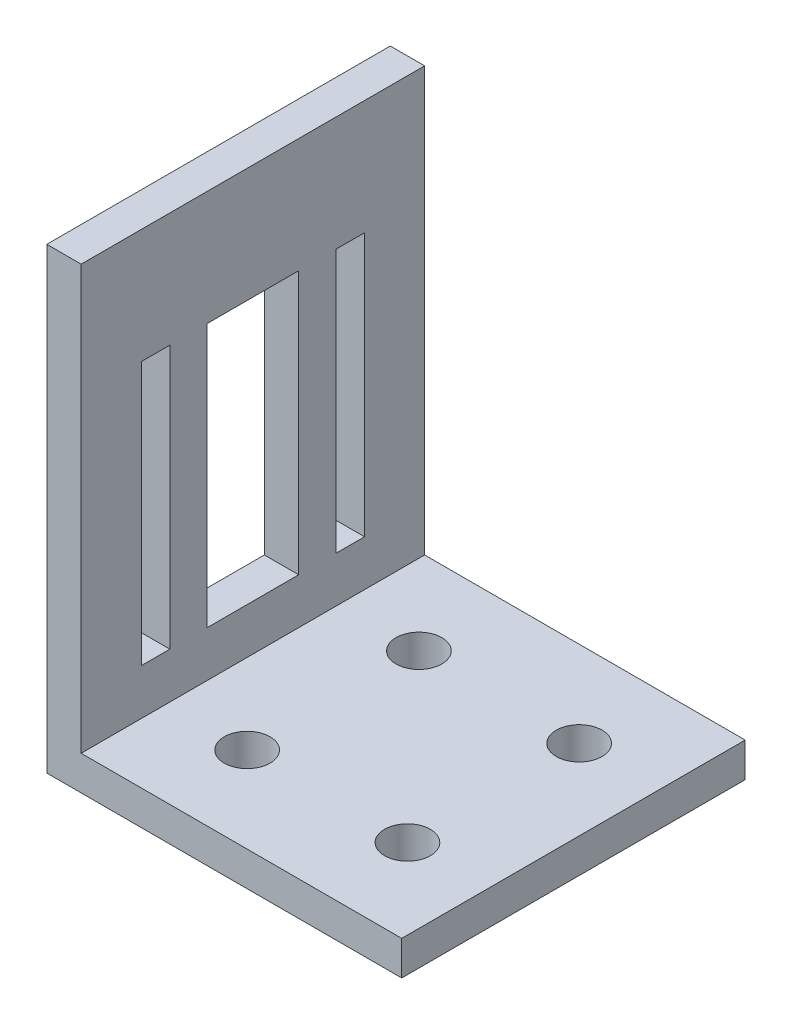
SolidWorks part; units mm, degrees
ref_plane "Front Plane" through (0, 0, 0) normal (0, 0, 1) x (1, 0, 0)
ref_plane "Top Plane" through (0, 0, 0) normal (0, 1, 0) x (1, 0, 0)
ref_plane "Right Plane" through (0, 0, 0) normal (1, 0, 0) x (0, 0, -1)
sketch "Sketch2" plane through (0, 0, 0) normal (0, 0, 1) x (1, 0, 0)
  line L0 (0, 0) -> (-31, 0)
  line L1 (-31, 0) -> (-31, 40)
  line L2 (0, 3) -> (-28, 3)
  line L3 (-28, 3) -> (-28, 40)
  line L4 (-28, 40) -> (-31, 40)
  line L5 (0, 0) -> (0, 3)
  dimension "D1" = 31
  dimension "D2" = 3
extrude "Boss-Extrude1" add sketch "Sketch2" along normal blind 30
sketch "Sketch3" plane through (0, 3, 0) normal (0, 1, 0) x (1, 0, 0)
  line L0 (-28, -15) -> (0, -15) construction
  line L1 (-14, -15) -> (0, -30) construction
  line L2 (-14, -30) -> (0, -15) construction
  line L5 (-28, -30) -> (-28, 0) construction
  line L6 (0, -30) -> (0, 0) construction
  line L7 (-14, 0) -> (-14, -30) construction
  line L8 (0, 0) -> (-28, 0) construction
  line L9 (0, -30) -> (-28, -30) construction
  circle A0 centre (-7, -22.5) radius 2
  circle A1 centre (-21, -22.5) radius 2
  circle A2 centre (-7, -7.5) radius 2
  circle A3 centre (-21, -7.5) radius 2
  point P24 (-7, -22.5)
  dimension "D1" = 4
extrude "Cut-Extrude1" cut sketch "Sketch3" against normal through all
sketch "Sketch5" plane through (-31, 0, 0) normal (-1, 0, 0) x (0, 0, 1)
  line L0 (15, 40) -> (15, 0) construction
  line L1 (30, 40) -> (0, 40) construction
  line L2 (30, 0) -> (0, 0) construction
  line L3 (23.5, 30) -> (23.5, 7) construction
  line L4 (24.75, 30) -> (24.75, 7)
  line L5 (19, 30) -> (19, 7)
  line L6 (22.25, 30) -> (22.25, 7)
  line L7 (22.25, 30) -> (24.75, 30)
  line L8 (24.75, 7) -> (22.25, 7)
  line L9 (19, 7) -> (11, 7)
  line L10 (19, 30) -> (11, 30)
  line L11 (7.75, 30) -> (5.25, 30)
  line L12 (5.25, 30) -> (5.25, 7)
  line L13 (5.25, 7) -> (7.75, 7)
  line L14 (7.75, 30) -> (7.75, 7)
  line L15 (11, 30) -> (11, 7)
  point P21 (15, 7)
  point P22 (15, 30)
  dimension "D1" = 10
  dimension "D2" = 7
  dimension "D3" = 1.25
  dimension "D4" = 4
  dimension "D5" = 8.5
extrude "Cut-Extrude2" cut sketch "Sketch5" against normal through all
